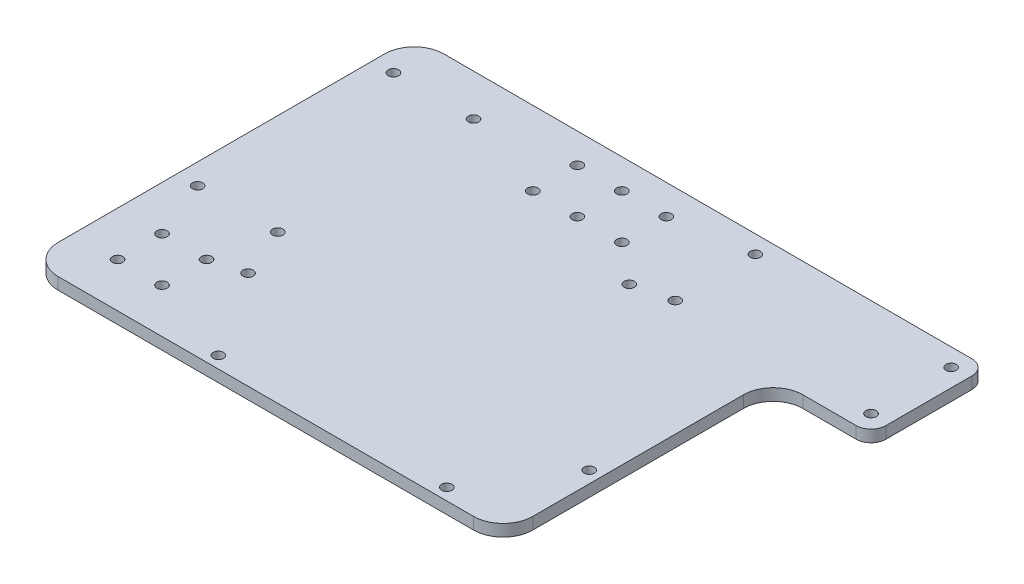
SolidWorks part; units mm, degrees
ref_plane "正面(Front)" through (0, 0, 0) normal (0, 0, 1) x (1, 0, 0)
ref_plane "平面(Top)" through (0, 0, 0) normal (0, 1, 0) x (1, 0, 0)
ref_plane "右側面(Right)" through (0, 0, 0) normal (1, 0, 0) x (0, 0, -1)
sketch "ｽｹｯﾁ1" plane through (0, 0, 0) normal (0, 1, 0) x (1, 0, 0)
  line L1 (-80, 65) -> (80, 65)
  line L2 (-80, 65) -> (-80, -65)
  line L3 (-80, -65) -> (80, -65)
  line L4 (80, 65) -> (80, -65)
  line L5 (-80, 65) -> (80, -65) construction
  line L6 (-80, -65) -> (80, 65) construction
  point P0 (0, 0)
  dimension "D1" = 160
  dimension "D2" = 130
extrude "ﾎﾞｽ - 押し出し1" add sketch "ｽｹｯﾁ1" along normal blind 4
sketch "ｽｹｯﾁ2" plane through (0, 4, 0) normal (0, 1, 0) x (1, 0, 0)
  line L0 (-80, -65) -> (80, -65) construction
  line L1 (-80, 65) -> (-80, -65) construction
  circle A0 centre (-73, -15) radius 1.75
  circle A1 centre (-73, 51) radius 1.75
  circle A2 centre (-46, -15) radius 1.75
  circle A3 centre (-46, 51) radius 1.75
  dimension "D1" = 3.5
  dimension "D2" = 50
  dimension "D3" = 7
  dimension "D4" = 66
  dimension "D5" = 27
extrude "ｶｯﾄ - 押し出し1" cut sketch "ｽｹｯﾁ2" against normal through all
sketch "ｽｹｯﾁ4" plane through (0, 4, 0) normal (0, 1, 0) x (1, 0, 0)
  line L0 (80, -65) -> (80, 65) construction
  line L1 (72, 25) -> (-35, 25) construction
  circle A0 centre (41, 59) radius 1.75
  circle A1 centre (41, 32) radius 1.75
  dimension "D1" = 3.5
  dimension "D2" = 27
  dimension "D3" = 39
  dimension "D4" = 7
extrude "ｶｯﾄ - 押し出し2" cut sketch "ｽｹｯﾁ4" against normal through all
sketch "ｽｹｯﾁ5" plane through (0, 4, 0) normal (0, 1, 0) x (1, 0, 0)
  line L0 (72, -57) -> (72, 25) construction
  line L1 (-80, -65) -> (80, -65) construction
  line L2 (-35, 25) -> (-35, -57) construction
  line L3 (-35, -57) -> (72, -57) construction
  line L4 (18.5, 25) -> (18.5, 86.7926) construction
  line L5 (72, 25) -> (-35, 25) construction
  circle A0 centre (57, -61) radius 1.75
  circle A1 centre (-20, -61) radius 1.75
  circle A2 centre (-39, -32) radius 1.75
  circle A3 centre (76, -32) radius 1.75
  circle A4 centre (28.5, 29) radius 1.75
  dimension "D1" = 15
  dimension "D2" = 3.5
  dimension "D3" = 4
  dimension "D4" = 15
  dimension "D5" = 4
  dimension "D7" = 4
  dimension "D8" = 25
  dimension "D9" = 4
  dimension "D10" = 4
  dimension "D11" = 10
  dimension "D6" = 25
extrude "ｶｯﾄ - 押し出し3" cut sketch "ｽｹｯﾁ5" against normal through all
sketch "ｽｹｯﾁ6" plane through (0, 4, 0) normal (0, 1, 0) x (1, 0, 0)
  line L0 (0, 0) -> (0, 80) construction
  line L1 (80, 65) -> (-80, 65) construction
  circle A0 centre (0, 55) radius 1.75
  circle A1 centre (0, 40) radius 1.75
  circle A2 centre (15, 55) radius 1.75
  circle A3 centre (15, 40) radius 1.75
  circle A4 centre (-15, 55) radius 1.75
  circle A5 centre (-15, 40) radius 1.75
  dimension "D1" = 3.5
  dimension "D2" = 15
  dimension "D3" = 10
  dimension "D5" = 15
  dimension "D7" = 15
  dimension "D4" = 2
  dimension "D6" = 2
extrude "ｶｯﾄ - 押し出し4" cut sketch "ｽｹｯﾁ6" against normal through all
sketch "ｽｹｯﾁ7" plane through (0, 4, 0) normal (0, 1, 0) x (1, 0, 0)
  line L0 (80, -65) -> (80, 65) construction
  line L1 (80, 65) -> (113, 65)
  line L2 (80, 65) -> (80, 26)
  line L3 (80, 26) -> (113, 26)
  line L4 (113, 65) -> (113, 26)
  line L5 (80, 65) -> (-80, 65) construction
  line L6 (110, 29) -> (110, 62) construction
  line L7 (38, 29) -> (110, 29) construction
  dimension "D1" = 3
  dimension "D2" = 3
extrude "ﾎﾞｽ - 押し出し2" add sketch "ｽｹｯﾁ7" against normal up to surface (4 mm away) up to face at (-15, 0, -53.25)
sketch "ｽｹｯﾁ8" plane through (0, 4, 0) normal (0, 1, 0) x (1, 0, 0)
  circle A0 centre (107, 59) radius 1.75
  circle A1 centre (107, 32) radius 1.75
  dimension "D1" = 3.5
extrude "ｶｯﾄ - 押し出し5" cut sketch "ｽｹｯﾁ8" against normal through all
fillet "ﾌｨﾚｯﾄ1" radius 10 4 edges at (80, 2, -26) (80, 2, 65) (-80, 2, 65) (-80, 2, -65)
fillet "ﾌｨﾚｯﾄ2" radius 5 2 edges at (113, 2, -65) (113, 2, -26)
sketch "ｽｹｯﾁ9" plane through (0, 4, 0) normal (0, 1, 0) x (1, 0, 0)
  line L0 (-70, -65) -> (70, -65) construction
  line L1 (-80, 55) -> (-80, -55) construction
  line L2 (-65, -50) -> (-65, -35) construction
  circle A0 centre (-65, -50) radius 1.75
  circle A1 centre (-50, -50) radius 1.75
  circle A2 centre (-65, -35) radius 1.75
  circle A3 centre (-50, -35) radius 1.75
  dimension "D1" = 15
  dimension "D2" = 15
  dimension "D3" = 3.5
  dimension "D4" = 15
  dimension "D6" = 15
  dimension "D5" = 2
extrude "ｶｯﾄ - 押し出し6" cut sketch "ｽｹｯﾁ9" against normal through all
